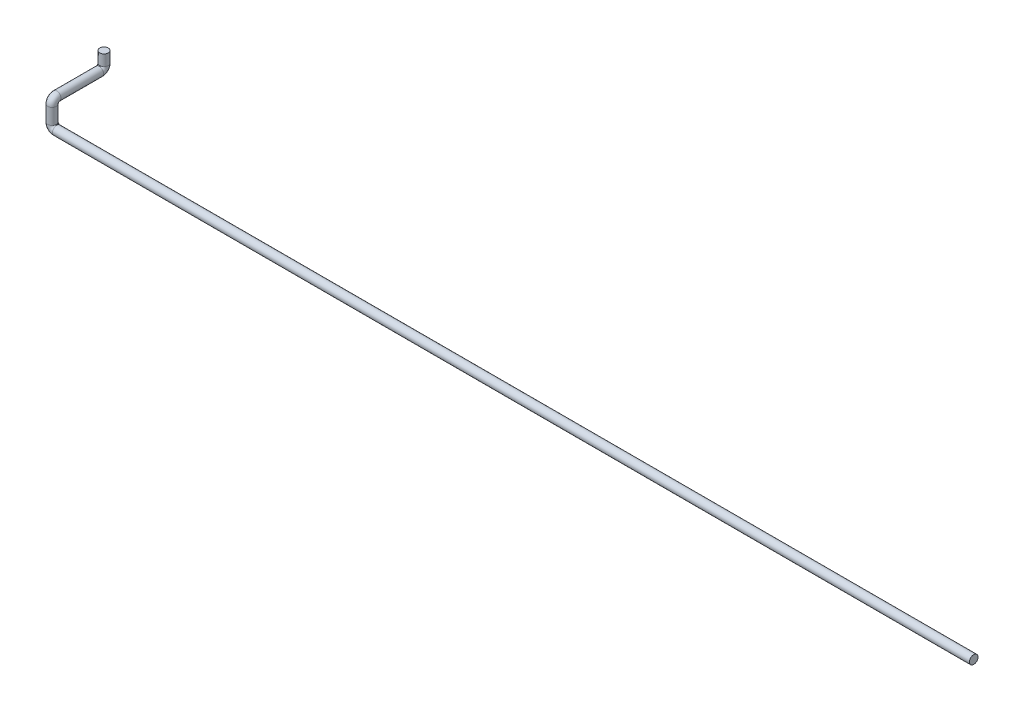
SolidWorks part; units mm, degrees
ref_plane "Alzado" through (0, 0, 0) normal (0, 0, 1) x (1, 0, 0)
ref_plane "Planta" through (0, 0, 0) normal (0, 1, 0) x (1, 0, 0)
ref_plane "Vista lateral" through (0, 0, 0) normal (1, 0, 0) x (0, 0, -1)
sketch3d "Croquis3D1"
  line L0 (0, 0, 0) -> (-2930, 0, 0)
  line L1 (-2945, 15, 0) -> (-2945, 65, 0)
  line L2 (-2945, 80, -15) -> (-2945, 80, -151)
  line L3 (-2945, 95, -166) -> (-2945, 130, -166)
  arc A0 (-2945, 80, -151) -> (-2945, 95, -166) centre (-2945, 95, -151) ccw
  arc A1 (-2945, 65, 0) -> (-2945, 80, -15) centre (-2945, 65, -15) ccw
  arc A2 (-2930, 0, 0) -> (-2945, 15, 0) centre (-2930, 15, 0) ccw
  point P8 (-2945, 80, -166)
  point P9 (-2930, 95, -151)
  point P12 (-2945, 80, 0)
  point P13 (-2960, 65, -15)
  point P16 (-2945, 0, 0)
  point P17 (-2930, 15, -15)
  dimension "D5" = 15
  dimension "D1" = 2945
  dimension "D2" = 80
  dimension "D3" = 166
  dimension "D4" = 50
sketch "Croquis1" plane through (0, 0, 0) normal (1, 0, 0) x (0, 0, -1)
  circle A0 centre (0, 0) radius 13.7
  dimension "D1" = 27.4
sweep "Barrer1" add profiles "Croquis1" path "Croquis3D1"
